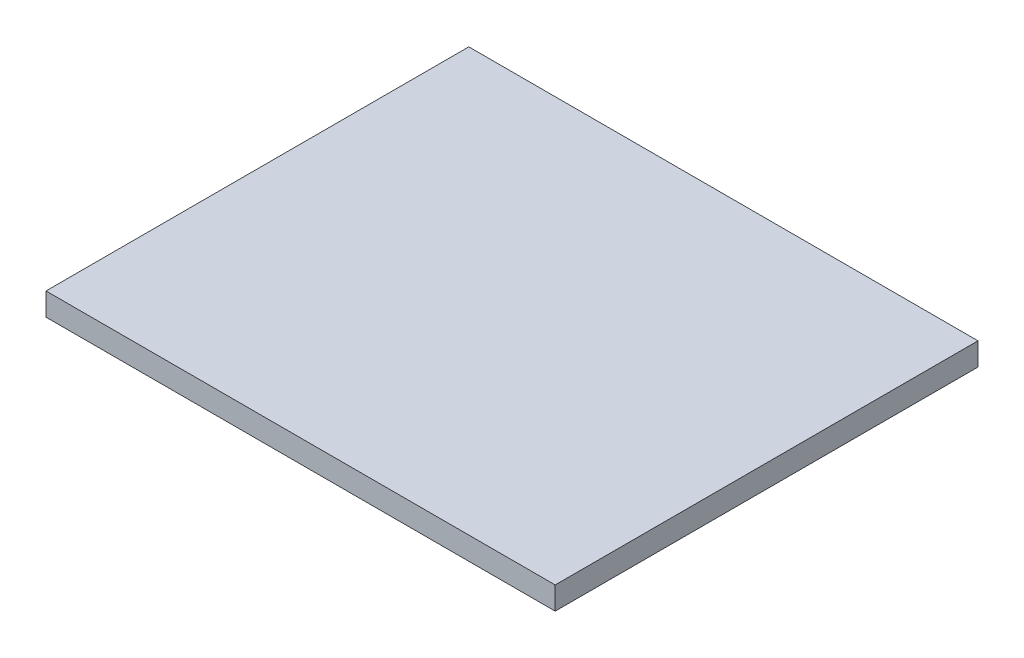
SolidWorks part; units mm, degrees
ref_plane "Front Plane" through (0, 0, 0) normal (0, 0, 1) x (1, 0, 0)
ref_plane "Top Plane" through (0, 0, 0) normal (0, 1, 0) x (1, 0, 0)
ref_plane "Right Plane" through (0, 0, 0) normal (1, 0, 0) x (0, 0, -1)
sketch "Sketch1" plane through (0, 0, 0) normal (0, 1, 0) x (1, 0, 0)
  line L1 (-28, 23.25) -> (28, 23.25)
  line L2 (-28, 23.25) -> (-28, -23.25)
  line L3 (-28, -23.25) -> (28, -23.25)
  line L4 (28, 23.25) -> (28, -23.25)
  line L5 (-28, 23.25) -> (28, -23.25) construction
  line L6 (-28, -23.25) -> (28, 23.25) construction
  point P0 (0, 0)
  dimension "D1" = 56
  dimension "D2" = 46.5
extrude "Boss-Extrude1" add sketch "Sketch1" along normal blind 2.5
sketch "Sketch2" plane through (0, 0, 0) normal (0, -1, 0) x (1, 0, 0)
  line L0 (25.5, -20.75) -> (25.5, 20.75)
  line L1 (25.5, 20.75) -> (-25.5, 20.75)
  line L2 (-25.5, 20.75) -> (-25.5, -20.75)
  line L3 (-25.5, -20.75) -> (25.5, -20.75)
  line L4 (28, -23.25) -> (28, 23.25)
  line L5 (28, 23.25) -> (-28, 23.25)
  line L6 (-28, 23.25) -> (-28, -23.25)
  line L7 (-28, -23.25) -> (28, -23.25)
  line L8 (28, -23.25) -> (28, 23.25) construction
  line L9 (28, 23.25) -> (-28, 23.25) construction
  line L10 (-28, 23.25) -> (-28, -23.25) construction
  line L11 (-28, -23.25) -> (28, -23.25) construction
  line L16 (23, -18.25) -> (23, 18.25)
  line L17 (23, 18.25) -> (-23, 18.25)
  line L18 (-23, 18.25) -> (-23, -18.25)
  line L19 (-23, -18.25) -> (23, -18.25)
  dimension "D1" = 0
  dimension "D2" = 2.5
  dimension "D3" = 2.5
extrude "Boss-Extrude2" add sketch "Sketch2" along normal blind 2.5
sketch "Sketch3" plane through (0, -2.5, 0) normal (0, -1, 0) x (1, 0, 0)
  line L0 (0, 20.75) -> (0, 0) construction
  line L1 (25.5, 20.75) -> (-25.5, 20.75) construction
  line L2 (0, 0) -> (25.5, 0) construction
  line L3 (25.5, -20.75) -> (25.5, 20.75) construction
  line L4 (25.5, 20.75) -> (-25.5, 20.75) construction
  line L5 (-3, 20.75) -> (3, 20.75)
  line L6 (-3, 20.75) -> (-3, 3)
  line L7 (-3, -20.75) -> (3, -20.75)
  line L8 (3, 20.75) -> (3, 3)
  line L9 (-25.5, -20.75) -> (25.5, -20.75) construction
  line L10 (-25.5, 20.75) -> (-25.5, -20.75) construction
  line L11 (25.5, 3) -> (3, 3)
  line L12 (25.5, 3) -> (25.5, -3)
  line L13 (25.5, -3) -> (3, -3)
  line L14 (-25.5, 3) -> (-25.5, -3)
  line L15 (-3, 3) -> (-25.5, 3)
  line L16 (-3, -3) -> (-25.5, -3)
  line L17 (-3, -3) -> (-3, -20.75)
  line L18 (3, -3) -> (3, -20.75)
  dimension "D1" = 6
  dimension "D2" = 6
  dimension "D3" = 3
  dimension "D4" = 3
extrude "Cut-Extrude1" cut sketch "Sketch3" against normal blind 2.5
fillet "Fillet1" radius 2 8 edges at (-24.25, 0, -3) (-3, 0, -19.5) (3, 0, -19.5) (-24.25, 0, 3) (24.25, 0, -3) (3, 0, 19.5) (24.25, 0, 3) (-3, 0, 19.5)
